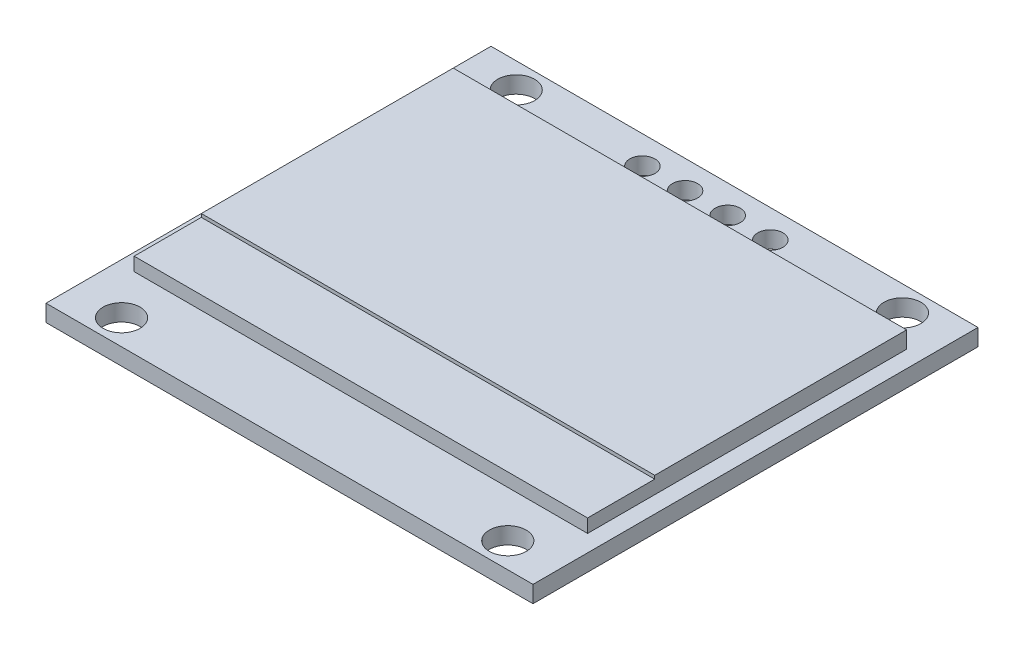
SolidWorks part; units mm, degrees
ref_plane "Front Plane" through (0, 0, 0) normal (0, 0, 1) x (1, 0, 0)
ref_plane "Top Plane" through (0, 0, 0) normal (0, 1, 0) x (1, 0, 0)
ref_plane "Right Plane" through (0, 0, 0) normal (1, 0, 0) x (0, 0, -1)
sketch "Sketch1" plane through (0, 0, 0) normal (0, 1, 0) x (1, 0, 0)
  line L5 (-14.5, 13.75) -> (14.5, 13.75)
  line L6 (-14.5, 13.75) -> (-14.5, -12.75)
  line L7 (-14.5, -12.75) -> (14.5, -12.75)
  line L8 (14.5, 13.75) -> (14.5, -12.75)
  dimension "D1" = 26.5
  dimension "D2" = 29
  dimension "D3" = 13.75
  dimension "D4" = 14.5
extrude "Boss-Extrude1" add sketch "Sketch1" along normal blind 1
sketch "Sketch2" plane through (0, 1, 0) normal (0, 1, 0) x (1, 0, 0)
  line L0 (14.5, 13.75) -> (-14.5, 13.75) construction
  circle A0 centre (-11.5, 12.25) radius 1.1
  circle A1 centre (11.5, 12.25) radius 1.1
  circle A2 centre (-11.5, -11.25) radius 1.1
  circle A3 centre (11.5, -11.25) radius 1.1
  point P8 (0, 0)
  point P11 (0.8466, -0.6626)
  dimension "D5" = 2.2
  dimension "D6" = 2.2
  dimension "D7" = 2.2
  dimension "D8" = 2.2
  dimension "D2" = 1.5
  dimension "D3" = 11.5
  dimension "D4" = 11.5
  dimension "D9" = 23.5
  dimension "D11" = 23
  dimension "D12" = 23
extrude "Cut-Extrude1" cut sketch "Sketch2" against normal blind 1
sketch "Sketch3" plane through (0, 1, 0) normal (0, 1, 0) x (1, 0, 0)
  line L0 (14.5, 13.75) -> (-14.5, 13.75) construction
  line L1 (-13.5, 10.5) -> (13.5, 10.5)
  line L2 (-13.5, 10.5) -> (-13.5, -4.5)
  line L3 (-13.5, -4.5) -> (13.5, -4.5)
  line L4 (13.5, 10.5) -> (13.5, -4.5)
  dimension "D1" = 3.25
  dimension "D2" = 27
  dimension "D3" = 13.5
  dimension "D4" = 15
extrude "Boss-Extrude2" add sketch "Sketch3" along normal blind 1
sketch "Sketch4" plane through (0, 1, 0) normal (0, 1, 0) x (1, 0, 0)
  line L1 (-13.5, 10.5) -> (13.5, 10.5)
  line L2 (-13.5, 10.5) -> (-13.5, -8.5)
  line L3 (-13.5, -8.5) -> (13.5, -8.5)
  line L4 (13.5, 10.5) -> (13.5, -8.5)
  dimension "D1" = 27
  dimension "D2" = 19
extrude "Boss-Extrude3" add sketch "Sketch4" along normal blind 0.8
sketch "Sketch5" plane through (0, 1, 0) normal (0, 1, 0) x (1, 0, 0)
  circle A0 centre (-1.27, 12.0736) radius 0.75
  circle A1 centre (1.27, 12.0736) radius 0.75
  circle A2 centre (3.81, 12.0736) radius 0.75
  circle A3 centre (-3.81, 12.0736) radius 0.75
  dimension "D5" = 1.5
  dimension "D6" = 1.5
  dimension "D7" = 1.5
  dimension "D8" = 1.5
  dimension "D1" = 2.54
  dimension "D2" = 1.27
  dimension "D3" = 1.27
  dimension "D4" = 2.54
extrude "Cut-Extrude2" cut sketch "Sketch5" against normal blind 10.8
